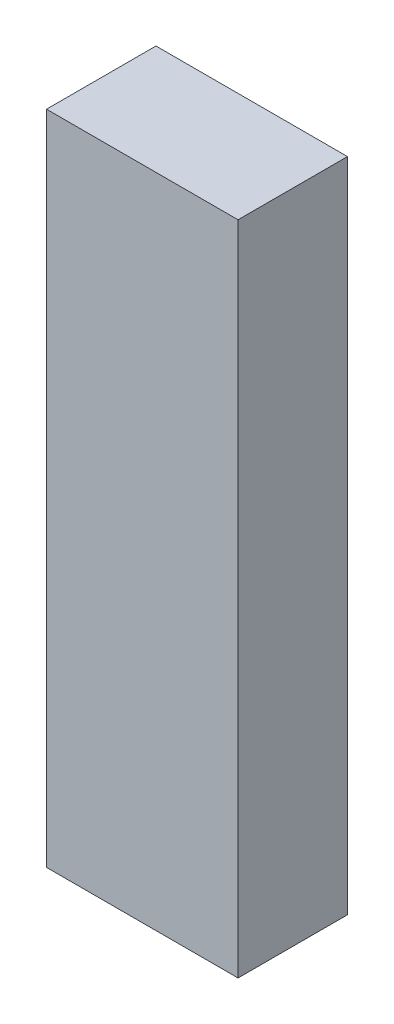
SolidWorks part; units mm, degrees
ref_plane "Front Plane" through (0, 0, 0) normal (0, 0, 1) x (1, 0, 0)
ref_plane "Top Plane" through (0, 0, 0) normal (0, 1, 0) x (1, 0, 0)
ref_plane "Right Plane" through (0, 0, 0) normal (1, 0, 0) x (0, 0, -1)
sketch "Sketch1" plane through (0, 0, 0) normal (0, 0, 1) x (1, 0, 0)
  line L1 (-7, 24) -> (7, 24)
  line L2 (-7, 24) -> (-7, -24)
  line L3 (-7, -24) -> (7, -24)
  line L4 (7, 24) -> (7, -24)
  point P4 (0, 24)
  point P6 (7, 0)
  dimension "D1" = 14
  dimension "D2" = 48
extrude "Boss-Extrude1" add sketch "Sketch1" along normal mid plane 8
